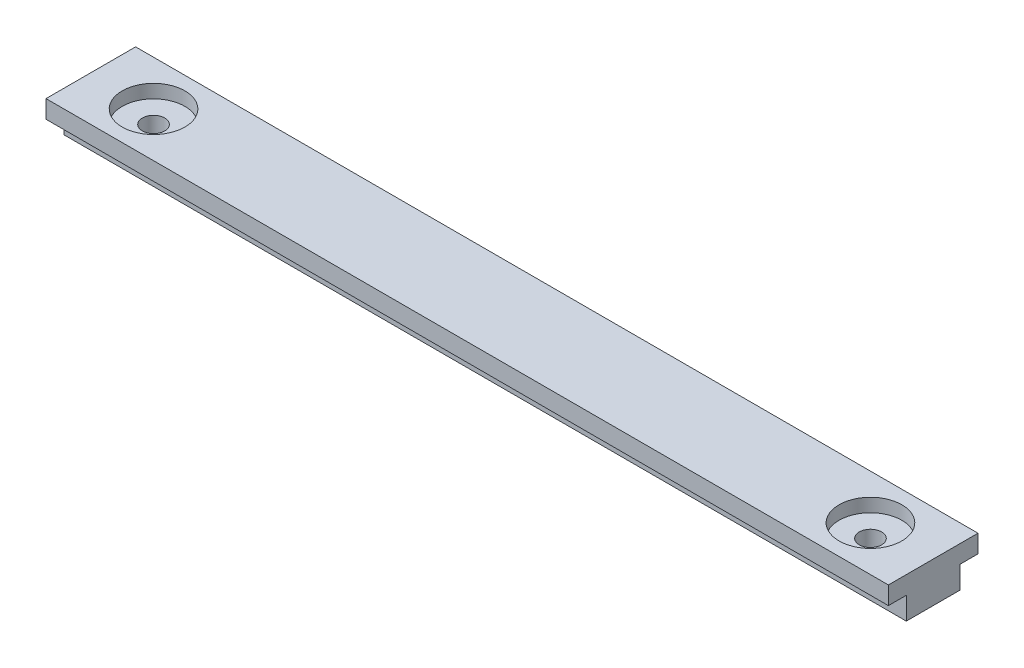
SolidWorks part; units mm, degrees
ref_plane "Front Plane" through (0, 0, 0) normal (0, 0, 1) x (1, 0, 0)
ref_plane "Top Plane" through (0, 0, 0) normal (0, 1, 0) x (1, 0, 0)
ref_plane "Right Plane" through (0, 0, 0) normal (1, 0, 0) x (0, 0, -1)
sketch "Sketch1" plane through (0, 0, 0) normal (0, 0, 1) x (1, 0, 0)
  line L0 (47, 0) -> (-47, 0)
  line L1 (-47, 0) -> (-47, -4.5)
  line L2 (47, -4.5) -> (-47, -4.5)
  line L6 (47, 0) -> (47, -4.5)
  point P13 (0, 0)
  dimension "D1" = 94
  dimension "D2" = 4.5
extrude "Main" add sketch "Sketch1" along normal mid plane 10
sketch "Sketch4" plane through (0, 0, 5) normal (0, 0, 1) x (1, 0, 0)
  line L0 (-47, -4.5) -> (47, -4.5)
  line L1 (47, -4.5) -> (47, -2)
  line L2 (47, -2) -> (-47, -2)
  line L3 (-47, -2) -> (-47, -4.5)
  line L5 (47, 0) -> (47, -4.5) construction
  line L6 (-47, -4.5) -> (-47, 0) construction
  line L7 (47, 0) -> (-47, 0) construction
  dimension "D1" = 2.5
  dimension "D2" = 2
  dimension "D3" = 94
  dimension "D4" = 94
extrude "WindowSlot1" cut sketch "Sketch4" against normal blind 2
mirror "Mirror1" about plane through (0, 0, 0) normal (0, 0, 1) of "WindowSlot1"
sketch "Sketch6" plane through (0, -4.5, 0) normal (0, 1, 0) x (0, 0, 1)
  circle A0 centre (0, 40) radius 1.25
  dimension "D1" = 2.5
  dimension "D2" = 40
extrude "Cut-Extrude2" cut sketch "Sketch6" along normal blind 3
pattern_linear "LPattern1" count 9 spacing 10 along (-1, 0, 0) of "Cut-Extrude2"
sketch "Sketch7" plane through (0, 0, 0) normal (0, 1, 0) x (0, 0, 1)
  circle A0 centre (0, 40) radius 3.5
  circle A2 centre (0, -40) radius 3.5
  dimension "D1" = 7
  dimension "D2" = 80
  dimension "D3" = 40
extrude "Cut-Extrude4" cut sketch "Sketch7" against normal blind 1.5
